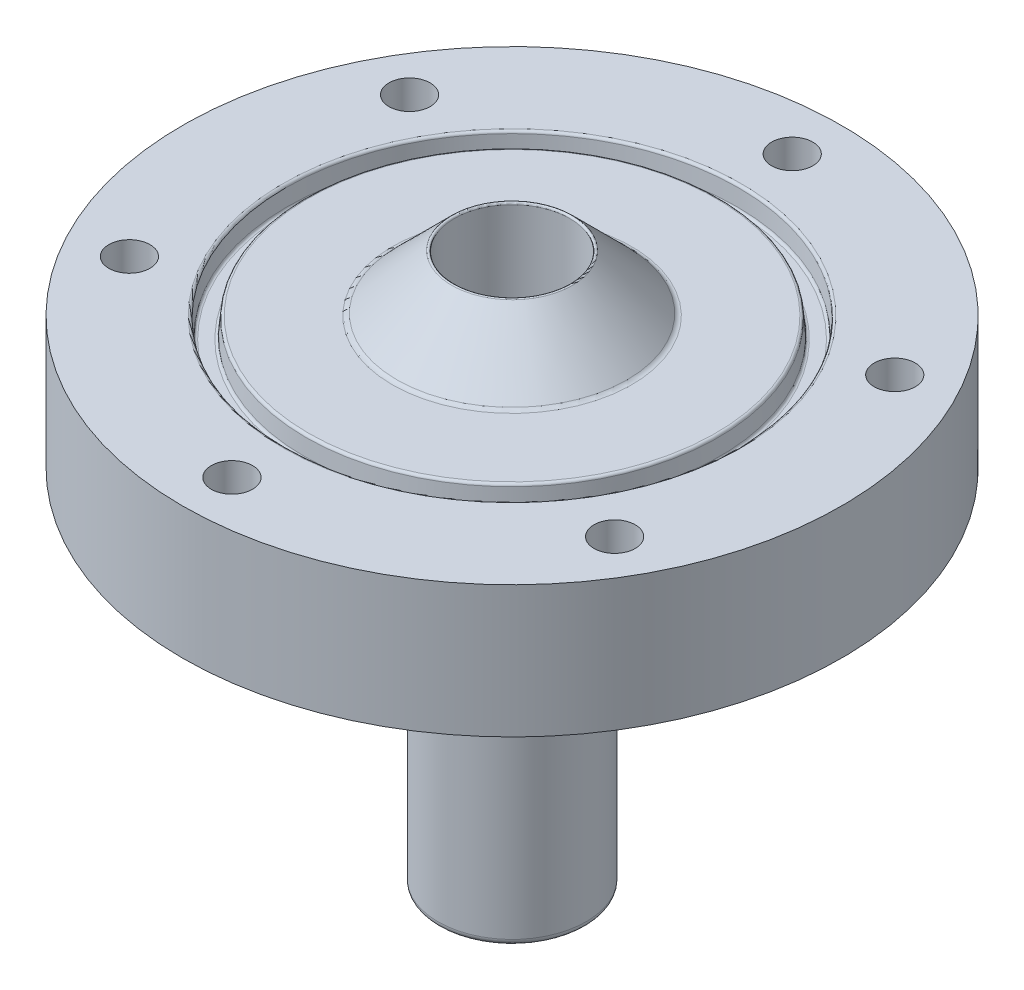
SolidWorks part; units mm, degrees
ref_plane "Front Plane" through (0, 0, 0) normal (0, 0, 1) x (1, 0, 0)
ref_plane "Top Plane" through (0, 0, 0) normal (0, 1, 0) x (1, 0, 0)
ref_plane "Right Plane" through (0, 0, 0) normal (1, 0, 0) x (0, 0, -1)
sketch "Sketch2" plane through (0, 0, 0) normal (0, 0, 1) x (1, 0, 0)
  line L0 (0, 31.1218) -> (0, -55.6083) construction
  line L1 (-5.715, -0.635) -> (-25.4, -0.635)
  line L2 (-4.445, 9.525) -> (-4.445, 14.097)
  line L3 (-9.017, 9.525) -> (-25.4, 9.525)
  line L5 (-25.4, 9.525) -> (-25.4, -0.635)
  line L7 (-4.445, 14.097) -> (-9.017, 9.525)
  line L9 (-4.445, 9.525) -> (-4.445, -28.575)
  line L12 (-4.445, 9.525) -> (-4.445, -28.575)
  line L13 (-4.445, -28.575) -> (-5.715, -28.575)
  line L14 (-5.715, -0.635) -> (-5.715, -28.575)
  line L15 (-4.445, 14.097) -> (-4.445, -28.575)
  line L19 (-25.4, 9.525) -> (-25.4, -0.635)
  line L20 (-25.4, -0.635) -> (-5.715, -0.635)
  line L25 (-25.4, -0.635) -> (-25.4, 9.525)
  line L26 (-5.715, -0.635) -> (-25.4, -0.635)
  dimension "D1" = 4.445
  dimension "D2" = 4.572
  dimension "D3" = 10.16
  dimension "D4" = 42.672
  dimension "D5" = 25.4
  dimension "D6" = 45
  dimension "D7" = 1.27
revolve "Revolve1" add sketch "Sketch2" angle 360 about L0
sketch "Sketch3" plane through (0, 9.525, 0) normal (0, 1, 0) x (1, 0, 0)
  circle A0 centre (0, 0) radius 15.875
  circle A1 centre (0, 0) radius 17.4625
extrude "Cut-Extrude1" cut sketch "Sketch3" against normal blind 1.5875 draft 5
fillet "Fillet2" radius 0.2032 4 edges at (0, 9.525, 17.4625) (0, 7.9375, 17.3236) (0, 9.525, 15.875) (0, 7.9375, 16.0139)
sketch "Sketch4" plane through (0, 9.525, 0) normal (0, 1, 0) x (1, 0, 0)
  circle A0 centre (0, 21.59) radius 1.5875
  circle A1 centre (18.6975, 10.795) radius 1.5875
  circle A2 centre (18.6975, -10.795) radius 1.5875
  circle A3 centre (0, -21.59) radius 1.5875
  circle A4 centre (-18.6975, -10.795) radius 1.5875
  circle A5 centre (-18.6975, 10.795) radius 1.5875
  point P15 (0, 0)
  dimension "D1" = 6
extrude "Cut-Extrude3" cut sketch "Sketch4" against normal up to next
fillet "Fillet3" radius 0.508 3 edges at (0, 9.525, 9.017) (0, -28.575, 5.715) (0, -0.635, 5.715)
fillet "Fillet4" radius 0.127 1 edges at (0, 14.097, 4.445)
